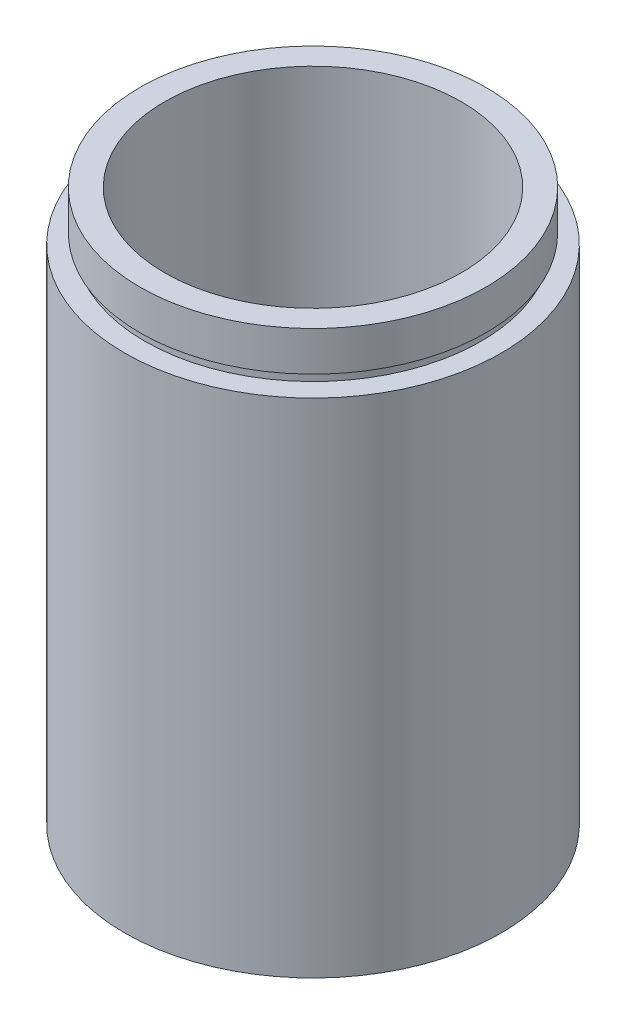
SolidWorks part; units mm, degrees
ref_plane "前视基准面" through (0, 0, 0) normal (0, 0, 1) x (1, 0, 0)
ref_plane "上视基准面" through (0, 0, 0) normal (0, 1, 0) x (1, 0, 0)
ref_plane "右视基准面" through (0, 0, 0) normal (1, 0, 0) x (0, 0, -1)
sketch "草图1" plane through (0, 0, 0) normal (0, 0, 1) x (1, 0, 0)
  line L0 (0, 161.3762) -> (0, 0) construction
  line L1 (141.7365, 0) -> (-131.7984, 0) construction
  line L2 (19.05, 0) -> (19.05, 50.8)
  line L3 (17, 4.5) -> (17.6, 4.5)
  line L4 (17, 0) -> (19.05, 0)
  line L5 (17.6, 4.5) -> (17.6, 5.5)
  line L6 (15, 5.5) -> (15, 55.8)
  line L7 (17, 4.5) -> (17, 0)
  line L8 (17.6, 5.5) -> (15, 5.5)
  line L9 (17, 51.8) -> (17, 50.8)
  line L10 (19.05, 50.8) -> (17, 50.8)
  line L11 (17.5, 51.8) -> (17.5, 55.8)
  line L12 (17, 51.8) -> (17.5, 51.8)
  line L13 (17.5, 55.8) -> (15, 55.8)
  dimension "D2" = 19.05
  dimension "D3" = 17.6
  dimension "D4" = 15
  dimension "D5" = 17
  dimension "D6" = 17.5
  dimension "D7" = 1
  dimension "D8" = 50.8
  dimension "D9" = 5
  dimension "D10" = 1
  dimension "D11" = 17
revolve "旋转1" add sketch "草图1" angle 360 about L0
cosmetic thread "装饰螺纹线1"
cosmetic thread "装饰螺纹线2"
cosmetic thread "装饰螺纹线3"
